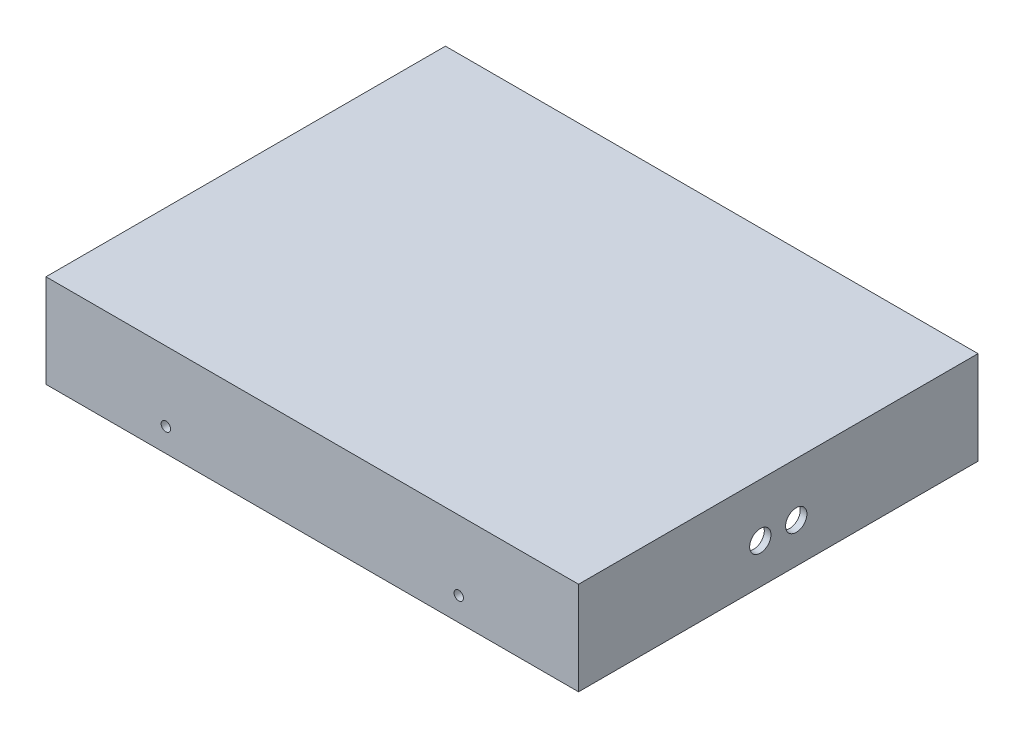
SolidWorks part; units mm, degrees
material "Acrylic (Medium-high impact)"
ref_plane "Front Plane" through (0, 0, 0) normal (0, 0, 1) x (1, 0, 0)
ref_plane "Top Plane" through (0, 0, 0) normal (0, 1, 0) x (1, 0, 0)
ref_plane "Right Plane" through (0, 0, 0) normal (1, 0, 0) x (0, 0, -1)
sketch "Sketch1" plane through (0, 0, 0) normal (0, 1, 0) x (1, 0, 0)
  line L1 (-200, 150) -> (200, 150)
  line L2 (-200, 150) -> (-200, -150)
  line L3 (-200, -150) -> (200, -150)
  line L4 (200, 150) -> (200, -150)
  line L5 (-200, 150) -> (200, -150) construction
  line L6 (-200, -150) -> (200, 150) construction
  point P0 (0, 0)
  dimension "D1" = 400
  dimension "D2" = 300
extrude "Boss-Extrude1" add sketch "Sketch1" along normal blind 70
sketch "Sketch2" plane through (0, 0, 0) normal (0, -1, 0) x (1, 0, 0)
  line L1 (-195, 145) -> (195, 145)
  line L2 (-195, 145) -> (-195, -145)
  line L3 (-195, -145) -> (195, -145)
  line L4 (195, 145) -> (195, -145)
  line L5 (-195, 145) -> (195, -145) construction
  line L6 (-195, -145) -> (195, 145) construction
  point P0 (0, 0)
  dimension "D1" = 390
  dimension "D2" = 290
extrude "Cut-Extrude1" cut sketch "Sketch2" against normal blind 60
fillet "Fillet2" radius 10 4 edges at (195, 30, 145) (195, 30, -145) (-195, 30, -145) (-195, 30, 145)
sketch "Sketch6" plane through (200, 0, 0) normal (1, 0, 0) x (0, 0, -1)
  circle A0 centre (-13.5, 30) radius 8
  circle A2 centre (13.5, 30) radius 8
  dimension "D2" = 16
extrude "Cut-Extrude3" cut sketch "Sketch6" against normal blind 10
sketch "Sketch7" plane through (0, 0, 150) normal (0, 0, 1) x (1, 0, 0)
  circle A0 centre (-110, 17.6701) radius 3.535
  circle A1 centre (110, 17.6701) radius 3.535
  dimension "D1" = 7.07
extrude "Cut-Extrude4" cut sketch "Sketch7" against normal blind 459
